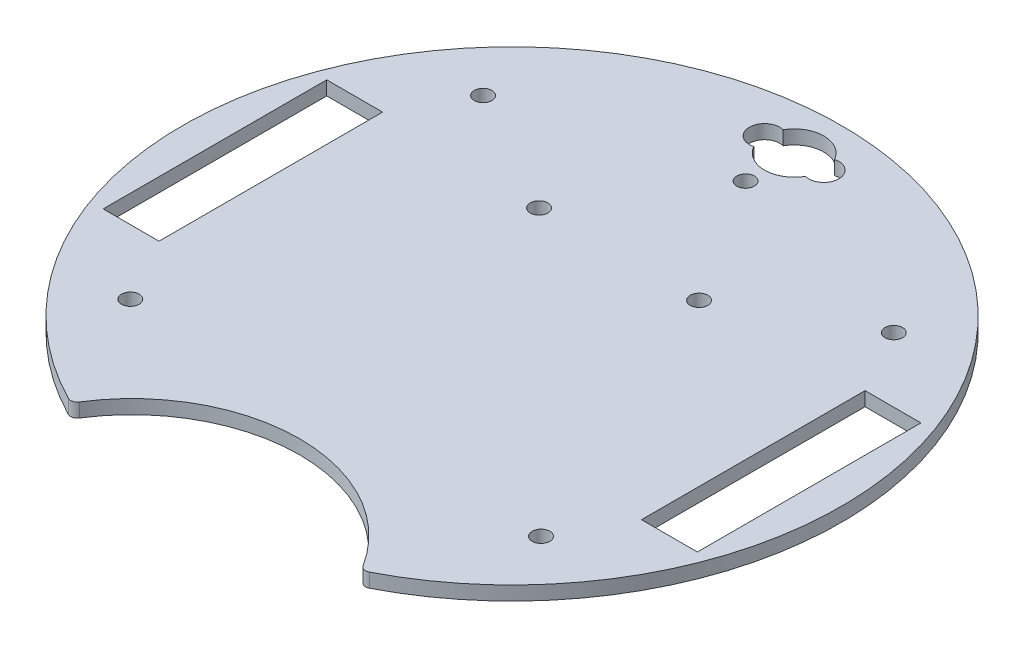
SolidWorks part; units mm, degrees
ref_plane "Front Plane" through (0, 0, 0) normal (0, 0, 1) x (1, 0, 0)
ref_plane "Top Plane" through (0, 0, 0) normal (0, 1, 0) x (1, 0, 0)
ref_plane "Right Plane" through (0, 0, 0) normal (1, 0, 0) x (0, 0, -1)
sketch "Sketch1" plane through (0, 0, 0) normal (0, 1, 0) x (1, 0, 0)
  line L1 (0, 86.2583) -> (0, -96.8543) construction
  line L3 (-32.9956, -67.352) -> (0, -86.402) construction
  line L4 (32.9956, -67.352) -> (0, -86.402) construction
  line L9 (54.8141, -25.4) -> (54.8141, 25.4)
  line L10 (-67.5141, -25.4) -> (-54.8141, -25.4)
  line L11 (-67.5141, -25.4) -> (-67.5141, 25.4)
  line L12 (-67.5141, 25.4) -> (-54.8141, 25.4)
  line L13 (-54.8141, 25.4) -> (-54.8141, -25.4)
  line L14 (67.5141, 25.4) -> (54.8141, 25.4)
  line L15 (67.5141, -25.4) -> (67.5141, 25.4)
  line L16 (67.5141, -25.4) -> (54.8141, -25.4)
  arc A1 (32.2407, -66.1006) -> (-32.2407, -66.1006) centre (0, -86.402) ccw
  arc A2 (34.1948, -66.6358) -> (-34.1948, -66.6358) centre (0, 0) ccw
  arc A3 (5.8576, 67.4236) -> (-5.8539, 67.4301) centre (0, 64.1077) ccw
  arc A4 (-5.8539, 67.4301) -> (-5.8539, 60.7853) centre (-6.731, 64.1077) ccw
  arc A5 (5.8576, 60.7918) -> (5.8576, 67.4236) centre (6.731, 64.1077) ccw
  arc A6 (-5.8539, 60.7853) -> (5.8576, 60.7918) centre (0, 64.1077) ccw
  circle A25 centre (-18.179, 24.3106) radius 2
  circle A38 centre (-46.6637, -40.0812) radius 2
  circle A39 centre (46.6637, -40.0812) radius 2
  circle A40 centre (46.6637, 40.0812) radius 2
  circle A41 centre (-46.6637, 40.0812) radius 2
  arc A42 (-34.1948, -66.6358) -> (-32.2407, -66.1006) centre (-33.51, -65.3013) ccw
  arc A43 (34.1948, -66.6358) -> (32.2407, -66.1006) centre (33.51, -65.3013) cw
  circle A44 centre (-6.731, 64.1077) radius 1.143
  circle A45 centre (6.731, 64.1077) radius 1.143
  circle A47 centre (18.179, 24.3106) radius 2
  circle A48 centre (0, 53.0612) radius 2
  dimension "D3" = 120
  dimension "D15" = 13.462
  dimension "D18" = 2.286
  dimension "D12" = 4
  dimension "D4" = 50.8
  dimension "D5" = 12.7
extrude "Boss-Extrude3" add sketch "Sketch1" along normal blind 3.175 contours A43 A2 A42 A1 A48 A47 A40 A39 A38 L15 L16 L9 L14 L12 L13 L10 L11 A6 A4 A3 A5 A25 A41
